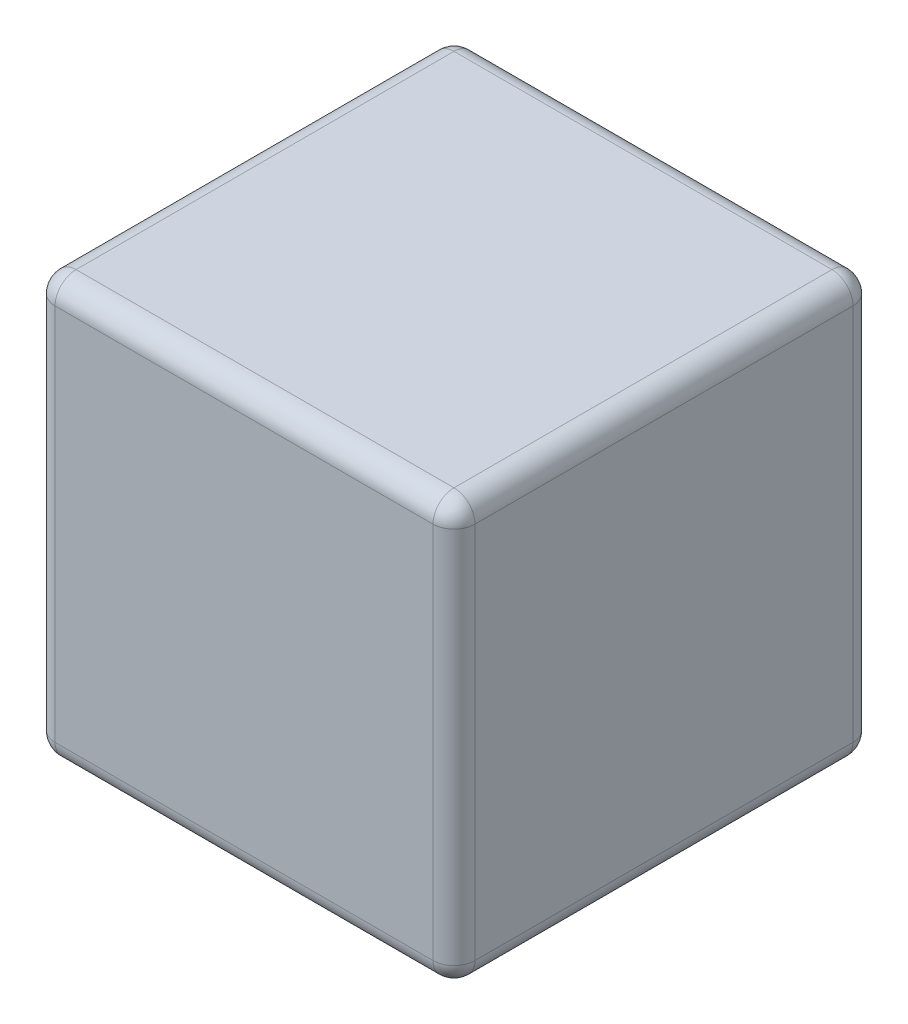
SolidWorks part; units mm, degrees
ref_plane "前视基准面" through (0, 0, 0) normal (0, 0, 1) x (1, 0, 0)
ref_plane "上视基准面" through (0, 0, 0) normal (0, 1, 0) x (1, 0, 0)
ref_plane "右视基准面" through (0, 0, 0) normal (1, 0, 0) x (0, 0, -1)
sketch "草图1" plane through (0, 0, 0) normal (0, 0, 1) x (1, 0, 0)
  line L1 (0, 0) -> (10, 0)
  line L2 (0, 0) -> (0, 10)
  line L3 (0, 10) -> (10, 10)
  line L4 (10, 0) -> (10, 10)
  dimension "D1" = 10
extrude "凸台-拉伸1" add sketch "草图1" along normal blind 10
fillet "圆角1" radius 0.5 12 edges at (0, 0, 5) (5, 0, 10) (0, 5, 10) (5, 0, 0) (0, 5, 0) (10, 0, 5) (10, 5, 10) (10, 5, 0) (10, 10, 5) (5, 10, 10) (0, 10, 5) (5, 10, 0)
